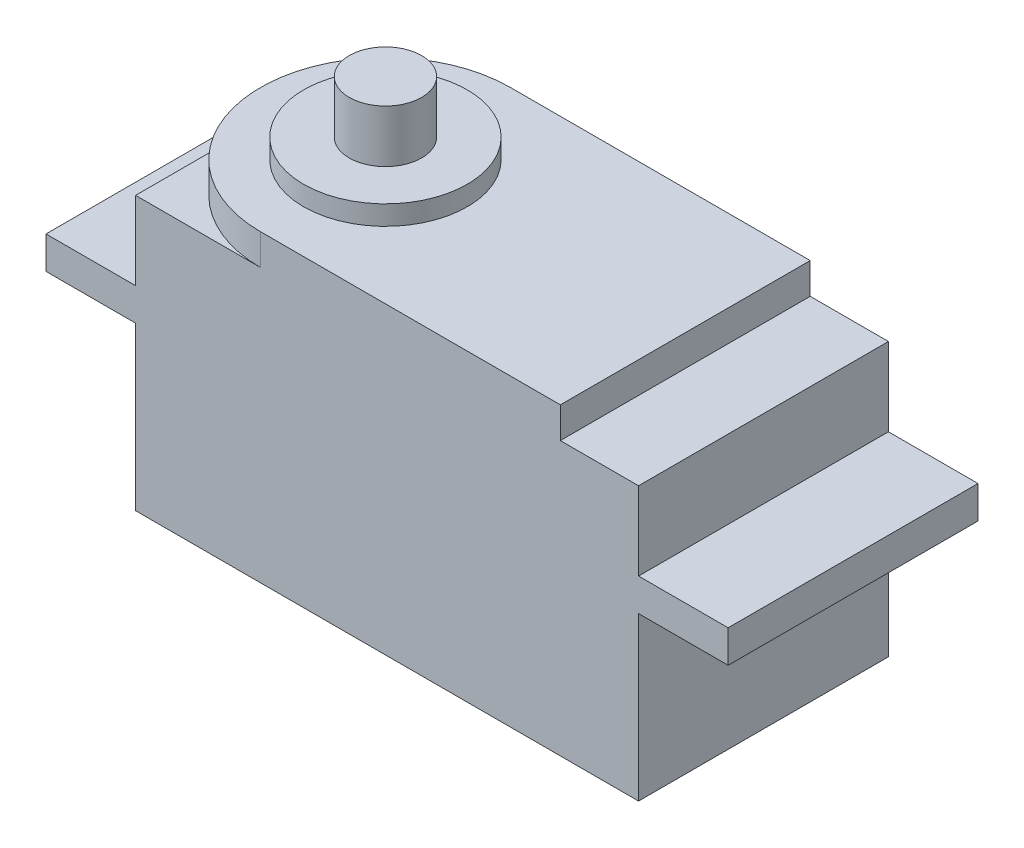
SolidWorks part; units mm, degrees
material "ABS"
ref_plane "Front Plane" through (0, 0, 0) normal (0, 0, 1) x (1, 0, 0)
ref_plane "Top Plane" through (0, 0, 0) normal (0, 1, 0) x (1, 0, 0)
ref_plane "Right Plane" through (0, 0, 0) normal (1, 0, 0) x (0, 0, -1)
sketch "Sketch1" plane through (0, 0, 0) normal (0, 1, 0) x (1, 0, 0)
  line L1 (-20.13, -10) -> (20.13, -10)
  line L2 (-20.13, -10) -> (-20.13, 10)
  line L3 (-20.13, 10) -> (20.13, 10)
  line L4 (20.13, -10) -> (20.13, 10)
  line L5 (-20.13, -10) -> (20.13, 10) construction
  line L6 (-20.13, 10) -> (20.13, -10) construction
  point P0 (0, 0)
  dimension "D1" = 20
  dimension "D2" = 40.26
extrude "Boss-Extrude1" add sketch "Sketch1" along normal blind 36.86
sketch "Sketch2" plane through (20.13, 0, 0) normal (1, 0, 0) x (0, 0, -1)
  line L0 (0, 36.86) -> (0, 0) construction
  line L1 (-10, 36.86) -> (10, 36.86) construction
  line L2 (10, 36.86) -> (10, 0) construction
  line L3 (-10, 28) -> (10, 28)
  line L4 (-10, 28) -> (-10, 30.6)
  line L5 (-10, 30.6) -> (10, 30.6)
  line L6 (10, 28) -> (10, 30.6)
  line L7 (-10, 28) -> (10, 30.6) construction
  line L8 (-10, 30.6) -> (10, 28) construction
  line L9 (-10, 0) -> (10, 0) construction
  point P5 (0, 29.3)
  dimension "D1" = 28
  dimension "D2" = 2.6
extrude "Boss-Extrude2" add sketch "Sketch2" along normal blind 7.17
sketch "Sketch3" plane through (-20.13, 0, 0) normal (-1, 0, 0) x (0, 0, 1)
  line L0 (0, 36.86) -> (0, 0) construction
  line L1 (-10, 36.86) -> (10, 36.86) construction
  line L2 (10, 36.86) -> (10, 0) construction
  line L3 (-10, 28) -> (10, 28)
  line L4 (-10, 28) -> (-10, 30.6)
  line L5 (-10, 30.6) -> (10, 30.6)
  line L6 (10, 28) -> (10, 30.6)
  line L7 (-10, 28) -> (10, 30.6) construction
  line L8 (-10, 30.6) -> (10, 28) construction
  line L9 (-10, 0) -> (10, 0) construction
  point P5 (0, 29.3)
  dimension "D1" = 2.6
  dimension "D2" = 28
extrude "Boss-Extrude3" add sketch "Sketch3" along normal blind 7.17
sketch "Sketch4" plane through (0, 36.86, 0) normal (0, 1, 0) x (1, 0, 0)
  line L0 (-20.13, 0) -> (20.13, 0) construction
  line L1 (-20.13, 10) -> (-20.13, -10) construction
  line L2 (20.13, -10) -> (20.13, 10) construction
  line L3 (0, 10) -> (0, -10) construction
  line L4 (20.13, 10) -> (-20.13, 10) construction
  line L5 (-20.13, -10) -> (20.13, -10) construction
  line L7 (-20.13, 10) -> (13.87, 10)
  line L8 (-20.13, 10) -> (-20.13, -10)
  line L9 (-20.13, -10) -> (13.87, -10)
  line L10 (13.87, 10) -> (13.87, -10)
  circle A0 centre (-10.13, 0) radius 10
  line M2 (20.13, 10) -> (-20.13, 10)
  dimension "D1" = 34
  dimension "D2" = 10
extrude "Boss-Extrude4" add sketch "Sketch4" along normal blind 2.48 contours A0 | A0 L9 L10 M2
sketch "Sketch5" plane through (0, 39.34, 0) normal (0, 1, 0) x (1, 0, 0)
  line L0 (-10.13, 10) -> (-10.13, -10) construction
  line L1 (13.87, 10) -> (-10.13, 10) construction
  arc A0 (-10.13, 10) -> (-10.13, -10) centre (-10.13, 0) ccw construction
  circle A1 centre (-10.13, 0) radius 6.55
  dimension "D1" = 13.1
extrude "Boss-Extrude5" add sketch "Sketch5" along normal blind 1.56
sketch "Sketch6" plane through (0, 40.9, 0) normal (0, 1, 0) x (1, 0, 0)
  line L0 (-10.13, 6.55) -> (-10.13, -6.55) construction
  circle A0 centre (-10.13, 0) radius 6.55 construction
  circle A1 centre (-10.13, 0) radius 6.55 construction
  circle A2 centre (-10.13, 0) radius 2.9
  dimension "D1" = 5.8
extrude "Boss-Extrude6" add sketch "Sketch6" along normal blind 4.2
sketch "Sketch7" plane through (0, 0, 0) normal (0, -1, 0) x (1, 0, 0)
  line L11 (20.13, -10) -> (20.13, 10)
  line L12 (20.13, 10) -> (-20.13, 10)
  line L13 (-20.13, 10) -> (-20.13, -10)
  line L14 (-20.13, -10) -> (20.13, -10)
  line L15 (20.13, -10) -> (20.13, 10)
  line L16 (20.13, 10) -> (-20.13, 10)
  line L17 (-20.13, 10) -> (-20.13, -10)
  line L18 (-20.13, -10) -> (20.13, -10)
  dimension "D1" = 0
extrude "Cut-Extrude1" cut sketch "Sketch7" against normal blind 15
